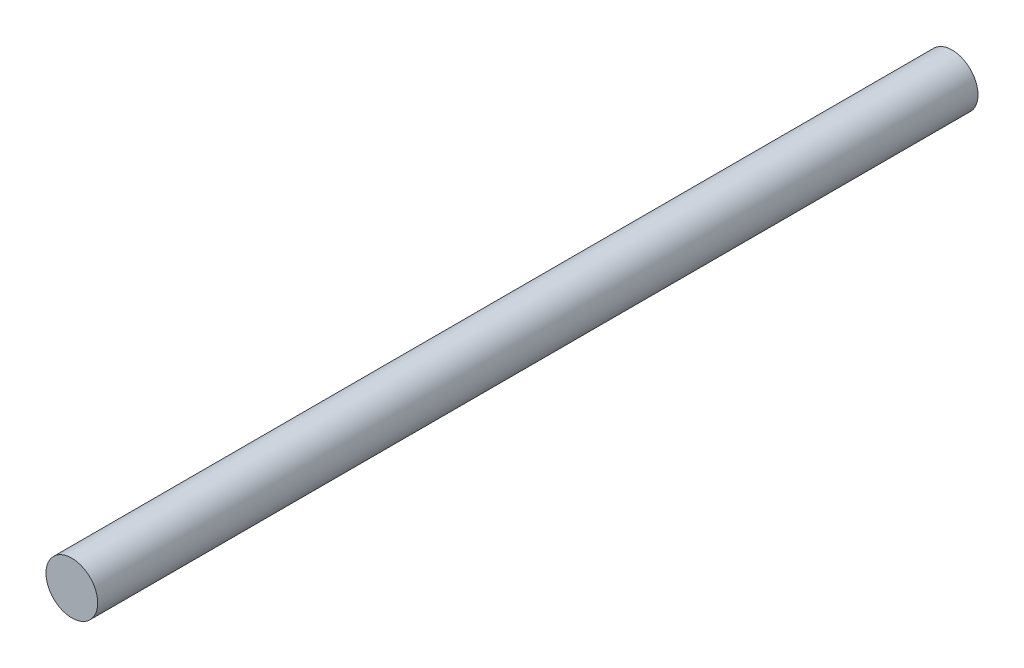
SolidWorks part; units mm, degrees
ref_plane "Ön Düzlem" through (0, 0, 0) normal (0, 0, 1) x (1, 0, 0)
ref_plane "Üst Düzlem" through (0, 0, 0) normal (0, 1, 0) x (1, 0, 0)
ref_plane "Sağ Düzlem" through (0, 0, 0) normal (1, 0, 0) x (0, 0, -1)
sketch "Çizim1" plane through (0, 0, 0) normal (0, 0, 1) x (1, 0, 0)
  circle A0 centre (0, 0) radius 2
  dimension "D1" = 4
extrude "Yükseklik-Ekstrüzyon1" add sketch "Çizim1" along normal blind 68
